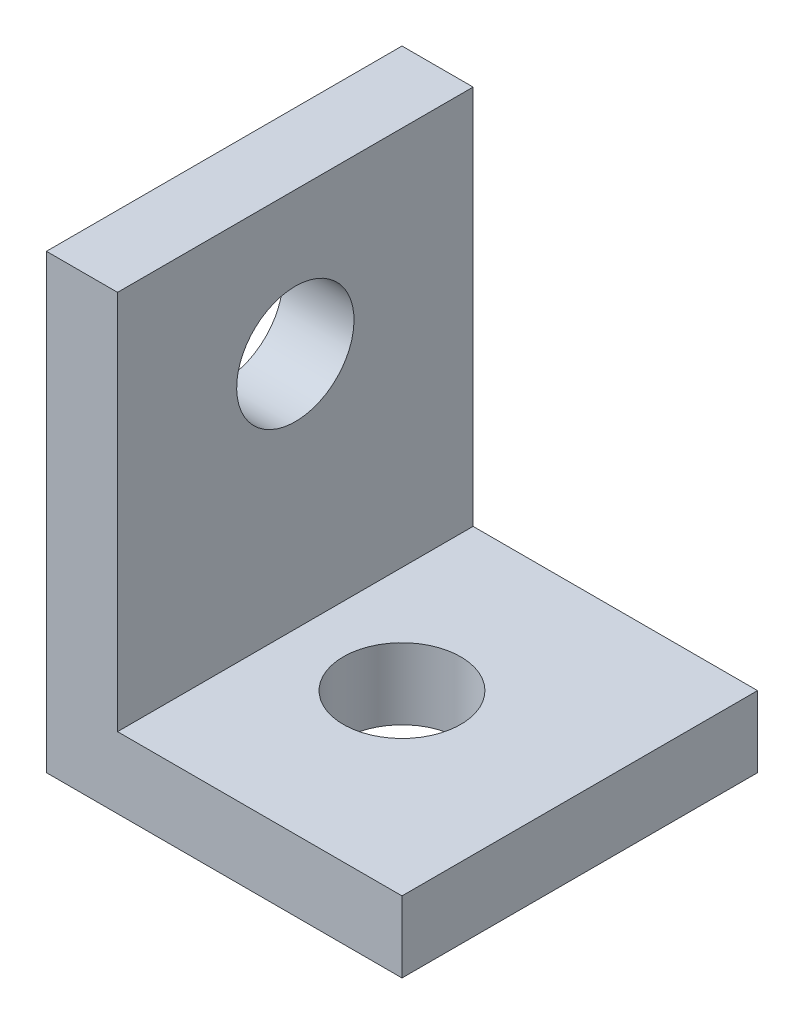
SolidWorks part; units mm, degrees
ref_plane "Front Plane" through (0, 0, 0) normal (0, 0, 1) x (1, 0, 0)
ref_plane "Top Plane" through (0, 0, 0) normal (0, 1, 0) x (1, 0, 0)
ref_plane "Right Plane" through (0, 0, 0) normal (1, 0, 0) x (0, 0, -1)
sketch "Sketch1" plane through (0, 0, 0) normal (0, 0, 1) x (1, 0, 0)
  line L0 (-5, 6.35) -> (-5, -6.35)
  line L1 (-5, -6.35) -> (5, -6.35)
  line L2 (5, -6.35) -> (5, -4.35)
  line L3 (5, -4.35) -> (-3, -4.35)
  line L4 (-3, -4.35) -> (-3, 6.35)
  line L5 (-3, 6.35) -> (-5, 6.35)
  line L6 (-5, -6.35) -> (5, 6.35) construction
  dimension "D1" = 2
  dimension "D2" = 12.7
  dimension "D3" = 10
extrude "Boss-Extrude1" add sketch "Sketch1" along normal mid plane 10
sketch "Sketch2" plane through (0, -4.35, 0) normal (0, 1, 0) x (1, 0, 0)
  line L1 (5, -5) -> (5, 5) construction
  circle A0 centre (0, 0) radius 1.65
  dimension "D1" = 3.3
  dimension "D2" = 5
extrude "Cut-Extrude1" cut sketch "Sketch2" against normal through all
sketch "Sketch3" plane through (-3, 0, 0) normal (1, 0, 0) x (0, 0, -1)
  line L2 (-5, 6.35) -> (5, 6.35) construction
  circle A0 centre (0, 2.35) radius 1.65
  dimension "D1" = 4
  dimension "D2" = 3.3
extrude "Cut-Extrude2" cut sketch "Sketch3" against normal blind 10
